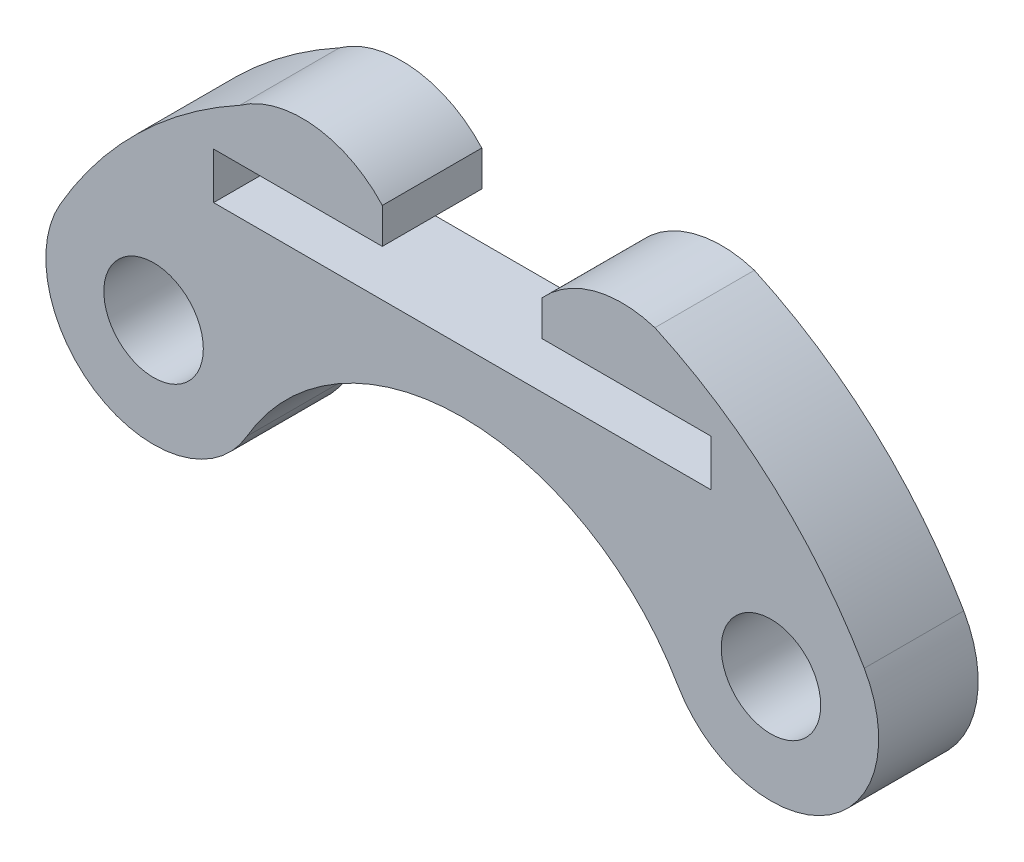
SolidWorks part; units mm, degrees
ref_plane "Plan de face" through (0, 0, 0) normal (0, 0, 1) x (1, 0, 0)
ref_plane "Plan de dessus" through (0, 0, 0) normal (0, 1, 0) x (1, 0, 0)
ref_plane "Plan de droite" through (0, 0, 0) normal (1, 0, 0) x (0, 0, -1)
sketch "Esquisse1" plane through (0, 0, 0) normal (0, 0, 1) x (1, 0, 0)
  line L0 (9.3098, 5.375) -> (7.6848, 2.5604) construction
  line L1 (-2.411, 11.8207) -> (-2.411, 10.75)
  line L2 (-9.3098, 5.375) -> (9.3098, 5.375) construction
  line L3 (2.411, 11.8207) -> (2.411, 10.75)
  line L4 (-7.6848, 2.5604) -> (-9.3098, 5.375) construction
  line L6 (-2.411, 10.75) -> (-7.5, 10.75)
  line L7 (2.411, 10.75) -> (7.5, 10.75)
  line L8 (7.5, 10.75) -> (7.5, 9.35)
  line L9 (7.5, 9.35) -> (-7.5, 9.35)
  line L10 (-7.5, 9.35) -> (-7.5, 10.75)
  arc A16 (5.8094, 12.7378) -> (2.411, 11.8207) centre (4.8221, 9.6414) ccw
  arc A17 (-2.411, 11.8207) -> (-6.7074, 12.2887) centre (-4.8221, 9.6414) ccw
  arc A18 (-6.7074, 12.2887) -> (-12.1244, 7) centre (0, 0) ccw
  arc A28 (12.1244, 7) -> (5.8094, 12.7378) centre (0, 0) ccw
  arc A30 (10.4906, 2.3471) -> (-10.4906, 2.3471) centre (0, 0) ccw construction
  circle A31 centre (9.3098, 5.375) radius 1.5
  circle A33 centre (-9.3098, 5.375) radius 1.5
  arc A34 (6.4952, 3.75) -> (12.1244, 7) centre (9.3098, 5.375) ccw
  arc A35 (-12.1244, 7) -> (-6.4952, 3.75) centre (-9.3098, 5.375) ccw
  arc A37 (6.4952, 3.75) -> (-6.4952, 3.75) centre (0, 0) ccw
  point P31 (0, 0)
  dimension "D2" = 14
  dimension "D3" = 6.5
  dimension "D4" = 1.4
  dimension "D5" = 3
  dimension "D8" = 14
  dimension "D9" = 3.25
  dimension "D10" = 6.5
  dimension "D11" = 3.25
  dimension "D12" = 18.6195
  dimension "D13" = 9.6441
  dimension "D6" = 3
  dimension "D16" = 6.192
  dimension "D7" = 60
  dimension "D14" = 10.78
  dimension "D15" = 10.78
  dimension "D17" = 15
  dimension "D18" = 1.4
  dimension "D19" = 5.089
  dimension "D20" = 5.089
  dimension "D21" = 1.0707
  dimension "D22" = 1.0707
  dimension "D23" = 9.35
extrude "Boss.-Extru.2" add sketch "Esquisse1" along normal blind 3
